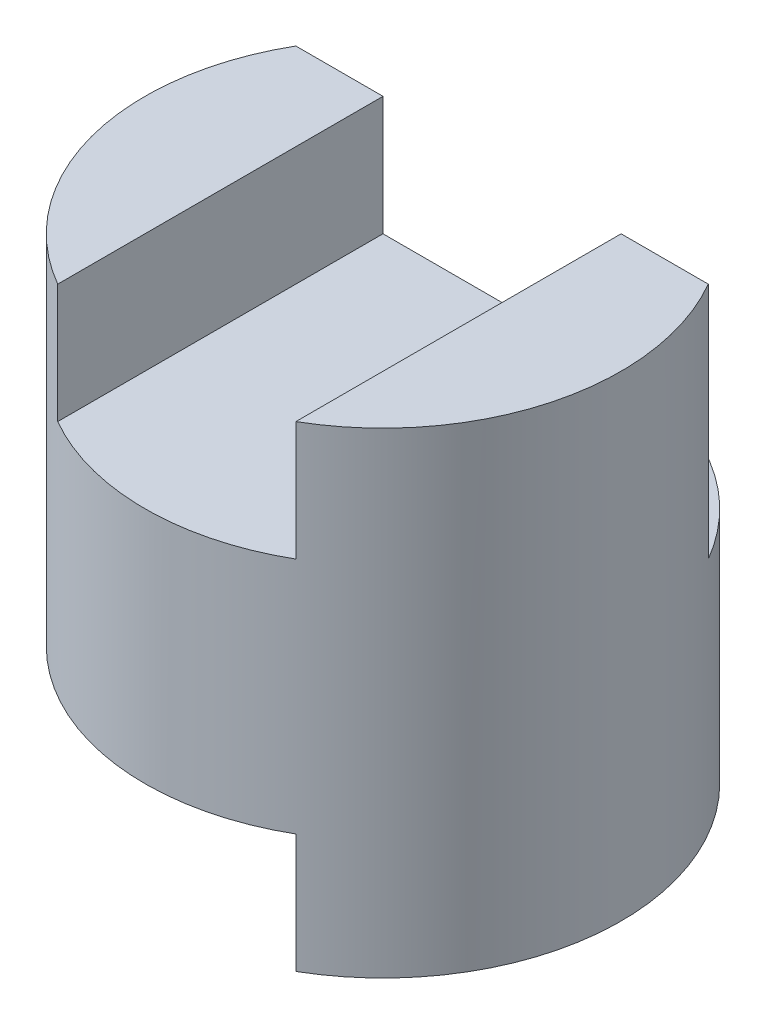
SolidWorks part; units mm, degrees
ref_plane "Front" through (0, 0, 0) normal (0, 0, 1) x (1, 0, 0)
ref_plane "Top" through (0, 0, 0) normal (0, 1, 0) x (1, 0, 0)
ref_plane "Right" through (0, 0, 0) normal (1, 0, 0) x (0, 0, -1)
sketch "Sketch1" plane through (0, 0, 0) normal (0, 1, 0) x (1, 0, 0)
  circle A0 centre (0, 0) radius 2
  dimension "D1" = 4
extrude "Boss-Extrude1" add sketch "Sketch1" along normal blind 4
sketch "Sketch2" plane through (0, 0, 0) normal (0, 0, 1) x (1, 0, 0)
  line L4 (1, 4) -> (1, 3)
  line L5 (1, 3) -> (-1, 3)
  line L6 (-1, 3) -> (-1, 4)
  line L9 (2, 4) -> (-2, 4) construction
  line L10 (-2, 0) -> (1, 0)
  line L11 (-2, 0) -> (-2, 1)
  line L12 (-2, 1) -> (1, 1)
  line L13 (1, 0) -> (1, 1)
  line L14 (-1, 4) -> (1, 4)
  dimension "D1" = 0
  dimension "D5" = 1
  dimension "D6" = 1
extrude "Cut-Extrude1" cut sketch "Sketch2" against normal blind 1 and the other way blind 3
sketch "Sketch3" plane through (0, 4, 0) normal (0, 1, 0) x (1, 0, 0)
  line L0 (-1.7321, 1) -> (1.7321, 1)
  arc A0 (-1.7321, 1) -> (1.7321, 1) centre (0, 0) cw
  point P5 (0, 0)
  point P6 (0, 0)
extrude "Cut-Extrude2" cut sketch "Sketch3" against normal blind 2
